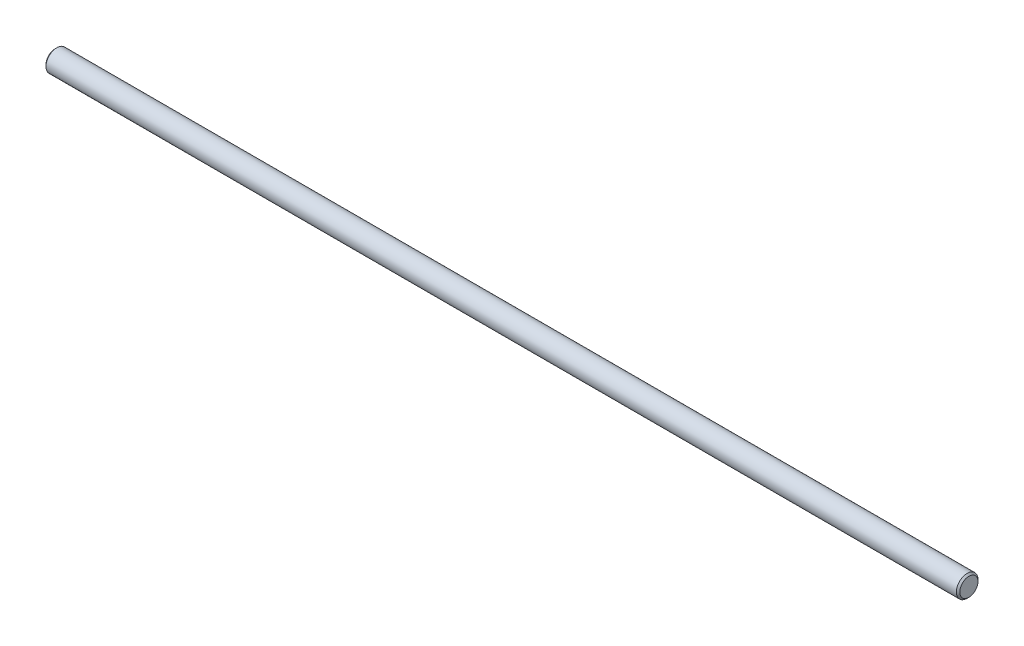
SolidWorks part; units mm, degrees
ref_plane "Front Plane" through (0, 0, 0) normal (0, 0, 1) x (1, 0, 0)
ref_plane "Top Plane" through (0, 0, 0) normal (0, 1, 0) x (1, 0, 0)
ref_plane "Right Plane" through (0, 0, 0) normal (1, 0, 0) x (0, 0, -1)
sketch "Sketch1" plane through (0, 0, 0) normal (1, 0, 0) x (0, 0, -1)
  circle A0 centre (0, 0) radius 6.35
  circle A1 centre (0, 0) radius 8
  dimension "D1" = 12.7
  dimension "D2" = 16
extrude "Boss-Extrude1" add sketch "Sketch1" along normal mid plane 536 contours A0
cosmetic thread "Cosmetic Thread1" parameters "D2"=10.072
cosmetic thread "Cosmetic Thread2" parameters "D2"=10.072
chamfer "Chamfer1" distance 1 angle 45 1 edges at (-268, 0, -6.35)
chamfer "Chamfer2" distance 1 angle 45 1 edges at (268, 0, -6.35)
